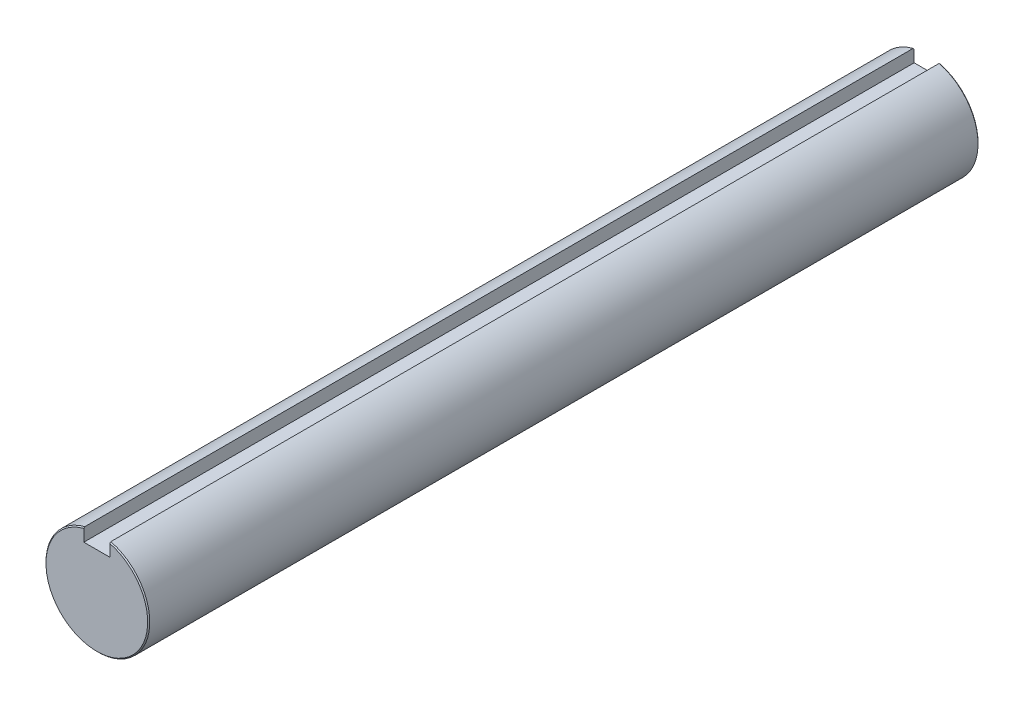
SolidWorks part; units mm, degrees
ref_plane "Front Plane" through (0, 0, 0) normal (0, 0, 1) x (1, 0, 0)
ref_plane "Top Plane" through (0, 0, 0) normal (0, 1, 0) x (1, 0, 0)
ref_plane "Right Plane" through (0, 0, 0) normal (1, 0, 0) x (0, 0, -1)
sketch "Sketch1" plane through (0, 0, 0) normal (1, 0, 0) x (0, 0, -1)
  line L0 (0, 0) -> (0, 4.7625) construction
  line L1 (-38.1, 4.7625) -> (38.1, 4.7625)
  line L2 (-38.1, 4.7625) -> (-38.1, -4.7625)
  line L3 (-38.1, -4.7625) -> (38.1, -4.7625)
  line L4 (38.1, 4.7625) -> (38.1, -4.7625)
  line L5 (-38.1, 4.7625) -> (38.1, -4.7625) construction
  line L6 (-38.1, -4.7625) -> (38.1, 4.7625) construction
  line L7 (0, 0) -> (0, -4.7625) construction
  line L8 (38.1, 4.7625) -> (-38.1, 4.7625) construction
  point P0 (0, 0)
  point P8 (-27.1463, 4.7625)
  point P10 (27.1463, 4.7625)
  point P11 (-23.495, -4.7625)
  point P12 (25.4517, -4.7625)
  point P15 (0, 4.7625)
  dimension "Diameter" = 9.525
  dimension "Length" = 76.2
  dimension "D1" = 10.9537
  dimension "D2" = 10.9537
  dimension "D3" = 14.605
  dimension "D4" = 12.6483
  dimension "Key Length" = 76.2
sketch "Sketch2" plane through (0, 0, 0) normal (0, 0, 1) x (1, 0, 0)
  line L0 (0, 0) -> (0, 4.7625) construction
  line L2 (1.1938, 3.4166) -> (-1.1938, 3.4166)
  line L3 (1.1938, 3.4166) -> (1.1938, 4.6104)
  line L4 (1.1938, 4.6104) -> (-1.1938, 4.6104)
  line L5 (-1.1938, 3.4166) -> (-1.1938, 4.6104)
  line L6 (1.1938, 3.4166) -> (-1.1938, 4.6104) construction
  line L7 (1.1938, 4.6104) -> (-1.1938, 3.4166) construction
  circle A0 centre (0, 0) radius 4.7625
  point P3 (0, 4.0135)
  dimension "Keyway Width" = 2.3876
  dimension "Keyway Depth" = 1.1938
sketch "Sketch3" plane through (0, 0, 0) normal (0, 0, 1) x (1, 0, 0)
  line L1 (-1.1938, 3.4166) -> (-1.1938, 4.6104) construction
  line L2 (1.1938, 3.4166) -> (-1.1938, 3.4166) construction
  line L3 (1.1938, 3.4166) -> (1.1938, 4.6104) construction
  line L5 (-1.1938, 3.4166) -> (-1.1938, 4.6104)
  line L6 (1.1938, 3.4166) -> (-1.1938, 3.4166)
  line L7 (1.1938, 3.4166) -> (1.1938, 4.6104)
  circle A0 centre (0, 0) radius 4.7625 construction
  arc A1 (-1.1938, 4.6104) -> (1.1938, 4.6104) centre (0, 0) ccw
extrude "Boss-Extrude1" add sketch "Sketch3" along normal up to vertex (38.1 mm away) and the other way up to vertex (38.1 mm away) up to point (0, 4.7625, 38.1) other way up to point (0, 4.7625, -38.1)
chamfer "Chamfer1" distance 0.0953 angle 45 2 edges at (0, -4.7625, 38.1) (0, -4.7625, -38.1)
equation "\"D2@Sketch1\"=1.15*\"Diameter@Sketch1\""
equation "\"D1@Sketch1\"=\"D2@Sketch1\""
equation "\"D3@Sketch1\"=\"D2@Sketch1\"*4/3"
equation "\"D4@Sketch1\"=\"D2@Sketch1\"/(tan(.5236*180/pi)*2)*4/3"
equation "\"D1@Chamfer1\"=\"Diameter@Sketch1\"*.01"
equation "\"Key Length@Sketch1\"=\"Length@Sketch1\""
